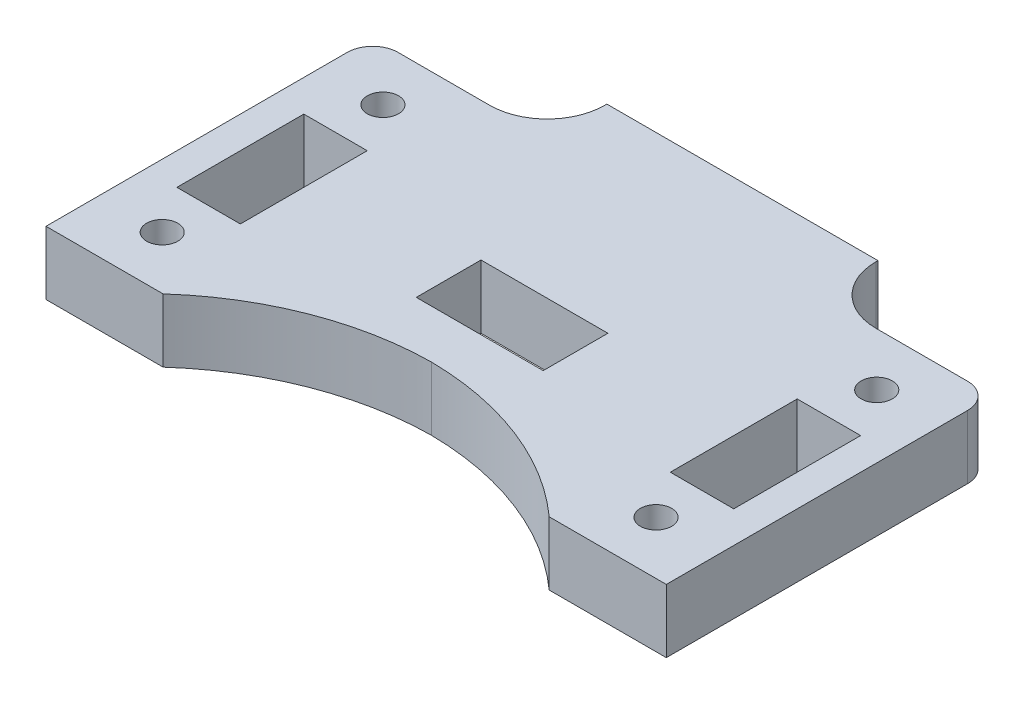
SolidWorks part; units mm, degrees
ref_plane "Front Plane" through (0, 0, 0) normal (0, 0, 1) x (1, 0, 0)
ref_plane "Top Plane" through (0, 0, 0) normal (0, 1, 0) x (1, 0, 0)
ref_plane "Right Plane" through (0, 0, 0) normal (1, 0, 0) x (0, 0, -1)
sketch "Sketch1" plane through (0, 0, 0) normal (0, 1, 0) x (1, 0, 0)
  line L0 (0, 22.3126) -> (0, 2.5006) construction
  line L1 (13.5681, 22.3126) -> (-13.5681, 22.3126)
  line L2 (-13.5681, 22.3126) -> (-13.5681, 22.0955)
  line L3 (-29.6847, -16.3436) -> (-19.3199, -16.3436)
  line L4 (21.5138, 6.2816) -> (27.8638, 6.2816)
  line L5 (20.0771, -11.0539) -> (29.6847, -16.3436) construction
  line L6 (-29.6847, -16.3436) -> (-20.0771, -11.0539) construction
  line L7 (0, -16.3436) -> (0, -6.4184) construction
  line L8 (-21.5138, 6.2816) -> (-27.8638, 6.2816)
  line L9 (-21.5138, 6.2816) -> (-21.5138, -6.4184)
  line L10 (-21.5138, -6.4184) -> (-27.8638, -6.4184)
  line L11 (-27.8638, 6.2816) -> (-27.8638, -6.4184)
  line L12 (-29.6847, -16.3436) -> (-31.0388, -16.3436)
  line L13 (-31.0388, -16.3436) -> (-31.0388, 16.3436)
  line L14 (-19.3199, 16.3436) -> (-31.0388, 16.3436)
  line L15 (31.0388, -16.3436) -> (31.0388, 16.3436)
  line L16 (29.6847, -16.3436) -> (31.0388, -16.3436)
  line L17 (27.8638, 6.2816) -> (27.8638, -6.4184)
  line L18 (21.5138, -6.4184) -> (27.8638, -6.4184)
  line L19 (21.5138, 6.2816) -> (21.5138, -6.4184)
  line L20 (-24.6888, 6.2816) -> (-24.6888, -20.9393) construction
  line L21 (-31.0388, -11.0539) -> (31.0388, -11.0539) construction
  line L22 (0, 16.3436) -> (0, 22.3126) construction
  line L23 (13.5681, 22.0955) -> (13.5681, 22.3126)
  line L24 (19.3199, 16.3436) -> (31.0388, 16.3436)
  line L25 (-6.35, 2.5006) -> (6.35, 2.5006)
  line L26 (-6.35, 2.5006) -> (-6.35, -3.9764)
  line L27 (-6.35, -3.9764) -> (6.35, -3.9764)
  line L28 (6.35, 2.5006) -> (6.35, -3.9764)
  line L29 (19.3199, -16.3436) -> (29.6847, -16.3436)
  circle A0 centre (-24.7096, 11.0441) radius 1.5621
  circle A1 centre (-24.7096, -11.0441) radius 1.5621
  circle A2 centre (24.7096, 11.0441) radius 1.5621
  circle A3 centre (24.7096, -11.0441) radius 1.5621
  arc A4 (-19.3199, 16.3436) -> (-13.5681, 22.0955) centre (-19.3199, 22.0955) ccw
  arc A5 (19.3199, 16.3436) -> (13.5681, 22.0955) centre (19.3199, 22.0955) cw
  arc A6 (0, -8.8228) -> (-19.3199, -16.3436) centre (0.32, -38.2204) ccw
  arc A7 (0, -8.8228) -> (19.3199, -16.3436) centre (-0.32, -38.2204) cw
  point P0 (0, 0)
  dimension "D3" = 3.1242
  dimension "D7" = 19.812
  dimension "D1" = 43.0276
  dimension "D2" = 6.35
  dimension "D4" = 3.175
  dimension "D5" = 12.7
  dimension "D6" = 5.969
  dimension "D8" = 12.7
  dimension "D9" = 6.35
  dimension "D10" = 6.477
extrude "Boss-Extrude1" add sketch "Sketch1" along normal blind 6.35
fillet "Fillet1" radius 2.54 2 edges at (-31.0388, 3.175, -16.3436) (31.0388, 3.175, -16.3436)
chamfer "Chamfer1" distance 1.905 angle 45 4 edges at (-24.7096, 0, 9.482) (24.7096, 0, 12.6062) (24.7096, 0, -12.6062) (-24.7096, 0, -9.482)
